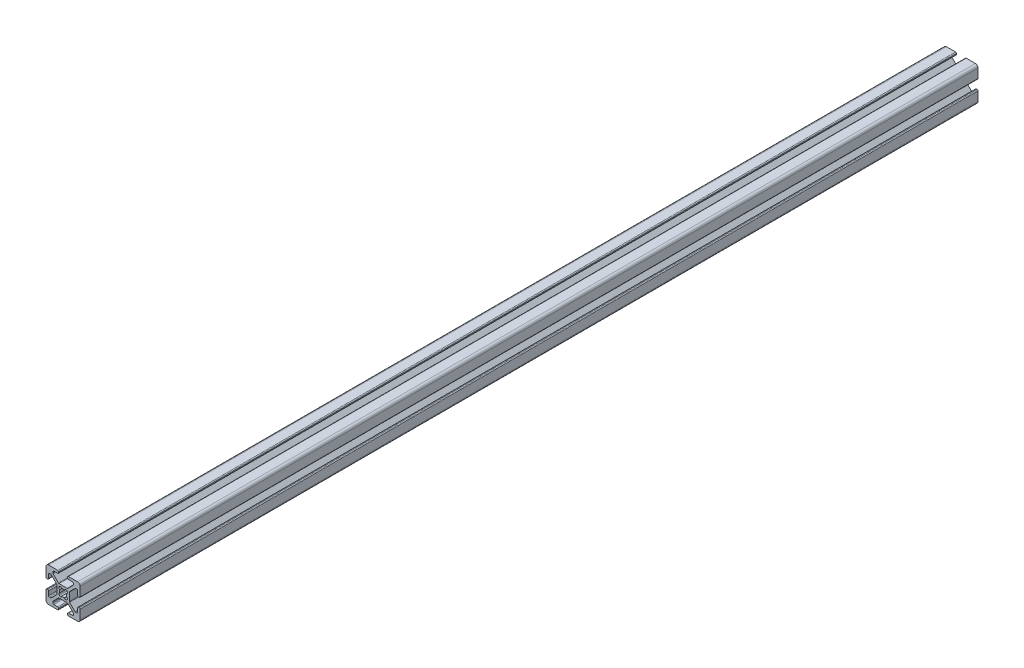
SolidWorks part; units mm, degrees
material "6061 Alloy"
ref_plane "Front Plane" through (0, 0, 0) normal (0, 0, 1) x (1, 0, 0)
ref_plane "Top Plane" through (0, 0, 0) normal (0, 1, 0) x (1, 0, 0)
ref_plane "Right Plane" through (0, 0, 0) normal (1, 0, 0) x (0, 0, -1)
ref_plane "Plane1" through (0, 0, 4000) normal (0, 0, 1) x (1, 0, 0)
sketch "Sketch1" plane through (0, 0, 4000) normal (0, 0, 1) x (1, 0, 0)
  line B0 (10, 3.138) -> (10, 8.5)
  line B1 (8.5, 10) -> (3.138, 10)
  line B2 (2.63, 9.492) -> (2.63, 9.008)
  line B3 (3.138, 8.5) -> (5.487, 8.5)
  line B4 (5.995, 7.992) -> (5.995, 7.2661)
  line B5 (5.8462, 6.9069) -> (2.7431, 3.8038)
  line B6 (2.3839, 3.655) -> (-2.3839, 3.655)
  line B7 (-2.7431, 3.8038) -> (-5.8462, 6.9069)
  line B8 (-5.995, 7.2661) -> (-5.995, 7.992)
  line B9 (-5.487, 8.5) -> (-3.138, 8.5)
  line B10 (-2.63, 9.008) -> (-2.63, 9.492)
  line B11 (-3.138, 10) -> (-8.5, 10)
  line B12 (-10, 8.5) -> (-10, 3.138)
  line B13 (-9.492, 2.63) -> (-9.008, 2.63)
  line B14 (-8.5, 3.138) -> (-8.5, 5.487)
  line B15 (-7.992, 5.995) -> (-7.2661, 5.995)
  line B16 (-6.9069, 5.8462) -> (-3.8038, 2.7431)
  line B17 (-3.655, 2.3839) -> (-3.655, -2.3839)
  line B18 (-3.8038, -2.7431) -> (-6.9069, -5.8462)
  line B19 (-7.2661, -5.995) -> (-7.992, -5.995)
  line B20 (-8.5, -5.487) -> (-8.5, -3.138)
  line B21 (-9.008, -2.63) -> (-9.492, -2.63)
  line B22 (-10, -3.138) -> (-10, -8.5)
  line B23 (-8.5, -10) -> (-3.138, -10)
  line B24 (-2.63, -9.492) -> (-2.63, -9.008)
  line B25 (-3.138, -8.5) -> (-5.487, -8.5)
  line B26 (-5.995, -7.992) -> (-5.995, -7.2661)
  line B27 (-5.8462, -6.9069) -> (-2.7431, -3.8038)
  line B28 (-2.3839, -3.655) -> (2.3839, -3.655)
  line B29 (2.7431, -3.8038) -> (5.8462, -6.9069)
  line B30 (5.995, -7.2661) -> (5.995, -7.992)
  line B31 (5.487, -8.5) -> (3.138, -8.5)
  line B32 (2.63, -9.008) -> (2.63, -9.492)
  line B33 (3.138, -10) -> (8.5, -10)
  line B34 (10, -8.5) -> (10, -3.138)
  line B35 (9.492, -2.63) -> (9.008, -2.63)
  line B36 (8.5, -3.138) -> (8.5, -5.487)
  line B37 (7.992, -5.995) -> (7.2661, -5.995)
  line B38 (6.9069, -5.8462) -> (3.8038, -2.7431)
  line B39 (3.655, -2.3839) -> (3.655, 2.3839)
  line B40 (3.8038, 2.7431) -> (6.9069, 5.8462)
  line B41 (7.2661, 5.995) -> (7.992, 5.995)
  line B42 (8.5, 5.487) -> (8.5, 3.138)
  line B43 (9.008, 2.63) -> (9.492, 2.63)
  line B44 (-2.1249, -2.3045) -> (-2.3045, -2.1249)
  line B45 (-2.3045, 2.1249) -> (-2.1249, 2.3045)
  line B46 (2.1249, 2.3045) -> (2.3045, 2.1249)
  line B47 (2.3045, -2.1249) -> (2.1249, -2.3045)
  arc B48 (9.492, 2.63) -> (10, 3.138) centre (9.492, 3.138) ccw
  arc B49 (10, 8.5) -> (8.5, 10) centre (8.5, 8.5) ccw
  arc B50 (3.138, 10) -> (2.63, 9.492) centre (3.138, 9.492) ccw
  arc B51 (2.63, 9.008) -> (3.138, 8.5) centre (3.138, 9.008) ccw
  arc B52 (5.487, 8.5) -> (5.995, 7.992) centre (5.487, 7.992) cw
  arc B53 (5.995, 7.2661) -> (5.8462, 6.9069) centre (5.487, 7.2661) cw
  arc B54 (2.7431, 3.8038) -> (2.3839, 3.655) centre (2.3839, 4.163) cw
  arc B55 (-2.3839, 3.655) -> (-2.7431, 3.8038) centre (-2.3839, 4.163) cw
  arc B56 (-5.8462, 6.9069) -> (-5.995, 7.2661) centre (-5.487, 7.2661) cw
  arc B57 (-5.995, 7.992) -> (-5.487, 8.5) centre (-5.487, 7.992) cw
  arc B58 (-3.138, 8.5) -> (-2.63, 9.008) centre (-3.138, 9.008) ccw
  arc B59 (-2.63, 9.492) -> (-3.138, 10) centre (-3.138, 9.492) ccw
  arc B60 (-8.5, 10) -> (-10, 8.5) centre (-8.5, 8.5) ccw
  arc B61 (-10, 3.138) -> (-9.492, 2.63) centre (-9.492, 3.138) ccw
  arc B62 (-9.008, 2.63) -> (-8.5, 3.138) centre (-9.008, 3.138) ccw
  arc B63 (-8.5, 5.487) -> (-7.992, 5.995) centre (-7.992, 5.487) cw
  arc B64 (-7.2661, 5.995) -> (-6.9069, 5.8462) centre (-7.2661, 5.487) cw
  arc B65 (-3.8038, 2.7431) -> (-3.655, 2.3839) centre (-4.163, 2.3839) cw
  arc B66 (-3.655, -2.3839) -> (-3.8038, -2.7431) centre (-4.163, -2.3839) cw
  arc B67 (-6.9069, -5.8462) -> (-7.2661, -5.995) centre (-7.2661, -5.487) cw
  arc B68 (-7.992, -5.995) -> (-8.5, -5.487) centre (-7.992, -5.487) cw
  arc B69 (-8.5, -3.138) -> (-9.008, -2.63) centre (-9.008, -3.138) ccw
  arc B70 (-9.492, -2.63) -> (-10, -3.138) centre (-9.492, -3.138) ccw
  arc B71 (-10, -8.5) -> (-8.5, -10) centre (-8.5, -8.5) ccw
  arc B72 (-3.138, -10) -> (-2.63, -9.492) centre (-3.138, -9.492) ccw
  arc B73 (-2.63, -9.008) -> (-3.138, -8.5) centre (-3.138, -9.008) ccw
  arc B74 (-5.487, -8.5) -> (-5.995, -7.992) centre (-5.487, -7.992) cw
  arc B75 (-5.995, -7.2661) -> (-5.8462, -6.9069) centre (-5.487, -7.2661) cw
  arc B76 (-2.7431, -3.8038) -> (-2.3839, -3.655) centre (-2.3839, -4.163) cw
  arc B77 (2.3839, -3.655) -> (2.7431, -3.8038) centre (2.3839, -4.163) cw
  arc B78 (5.8462, -6.9069) -> (5.995, -7.2661) centre (5.487, -7.2661) cw
  arc B79 (5.995, -7.992) -> (5.487, -8.5) centre (5.487, -7.992) cw
  arc B80 (3.138, -8.5) -> (2.63, -9.008) centre (3.138, -9.008) ccw
  arc B81 (2.63, -9.492) -> (3.138, -10) centre (3.138, -9.492) ccw
  arc B82 (8.5, -10) -> (10, -8.5) centre (8.5, -8.5) ccw
  arc B83 (10, -3.138) -> (9.492, -2.63) centre (9.492, -3.138) ccw
  arc B84 (9.008, -2.63) -> (8.5, -3.138) centre (9.008, -3.138) ccw
  arc B85 (8.5, -5.487) -> (7.992, -5.995) centre (7.992, -5.487) cw
  arc B86 (7.2661, -5.995) -> (6.9069, -5.8462) centre (7.2661, -5.487) cw
  arc B87 (3.8038, -2.7431) -> (3.655, -2.3839) centre (4.163, -2.3839) cw
  arc B88 (3.655, 2.3839) -> (3.8038, 2.7431) centre (4.163, 2.3839) cw
  arc B89 (6.9069, 5.8462) -> (7.2661, 5.995) centre (7.2661, 5.487) cw
  arc B90 (7.992, 5.995) -> (8.5, 5.487) centre (7.992, 5.487) cw
  arc B91 (8.5, 3.138) -> (9.008, 2.63) centre (9.008, 3.138) ccw
  arc B92 (0.804, -1.9351) -> (-0.804, -1.9351) centre (0, 0) cw
  arc B93 (-0.804, -1.9351) -> (-2.1249, -2.3045) centre (-1.5684, -1.748) cw
  arc B94 (-2.3045, -2.1249) -> (-1.9351, -0.804) centre (-1.748, -1.5684) cw
  arc B95 (-1.9351, -0.804) -> (-1.9351, 0.804) centre (0, 0) cw
  arc B96 (-1.9351, 0.804) -> (-2.3045, 2.1249) centre (-1.748, 1.5684) cw
  arc B97 (-2.1249, 2.3045) -> (-0.804, 1.9351) centre (-1.5684, 1.748) cw
  arc B98 (-0.804, 1.9351) -> (0.804, 1.9351) centre (0, 0) cw
  arc B99 (0.804, 1.9351) -> (2.1249, 2.3045) centre (1.5684, 1.748) cw
  arc B100 (2.3045, 2.1249) -> (1.9351, 0.804) centre (1.748, 1.5684) cw
  arc B101 (1.9351, 0.804) -> (1.9351, -0.804) centre (0, 0) cw
  arc B102 (1.9351, -0.804) -> (2.3045, -2.1249) centre (1.748, -1.5684) cw
  arc B103 (2.1249, -2.3045) -> (0.804, -1.9351) centre (1.5684, -1.748) cw
sketch_block_instance "Block1-1"
sketch_block "Block1"
extrude "Boss-Extrude1" add sketch "Sketch1" against normal blind 525
